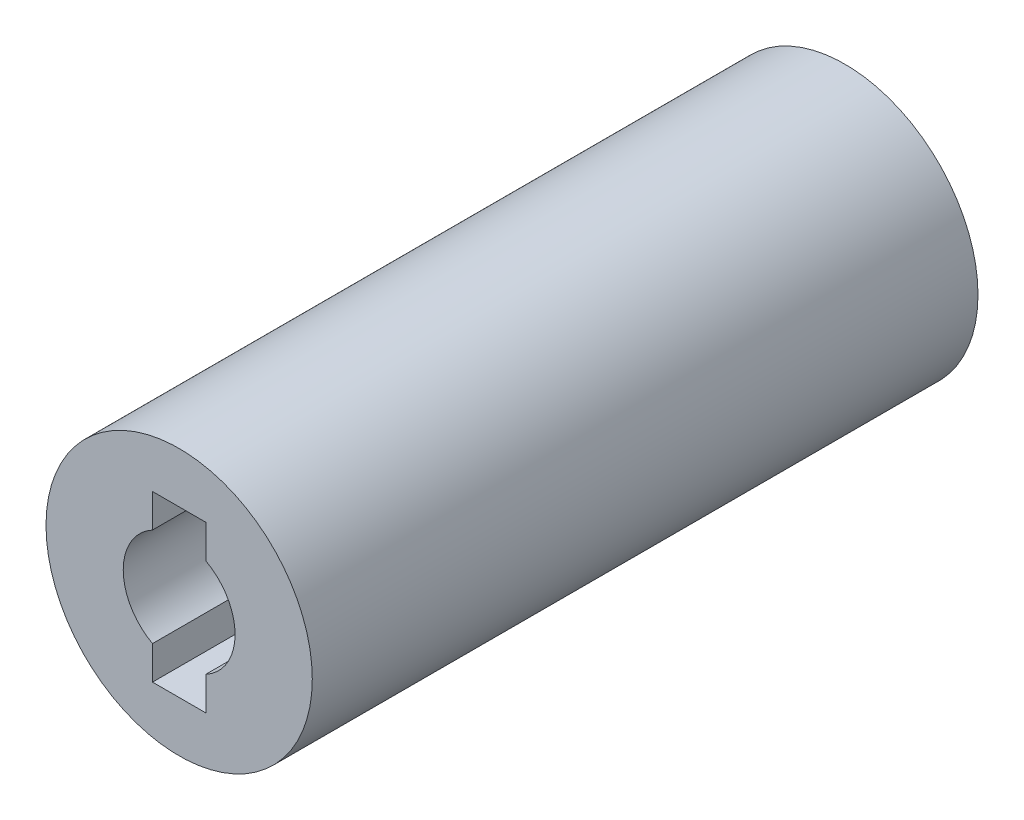
SolidWorks part; units mm, degrees
ref_plane "Front Plane" through (0, 0, 0) normal (0, 0, 1) x (1, 0, 0)
ref_plane "Top Plane" through (0, 0, 0) normal (0, 1, 0) x (1, 0, 0)
ref_plane "Right Plane" through (0, 0, 0) normal (1, 0, 0) x (0, 0, -1)
sketch "Sketch1" plane through (0, 0, 0) normal (0, 0, 1) x (1, 0, 0)
  circle A0 centre (0, 0) radius 5
  dimension "D1" = 10
extrude "Boss-Extrude1" add sketch "Sketch1" along normal blind 25
sketch "Sketch2" plane through (0, 0, 25) normal (0, 0, 1) x (1, 0, 0)
  circle A0 centre (0, 0) radius 2.1
  dimension "D1" = 4.2
extrude "Cut-Extrude1" cut sketch "Sketch2" against normal blind 10
sketch "Sketch3" plane through (0, 0, 25) normal (0, 0, 1) x (1, 0, 0)
  line L1 (-1, 3.1) -> (1, 3.1)
  line L2 (-1, 3.1) -> (-1, -3.1)
  line L3 (-1, -3.1) -> (1, -3.1)
  line L4 (1, 3.1) -> (1, -3.1)
  point P4 (0, 3.1)
  point P5 (-1, 0)
  dimension "D1" = 2
  dimension "D2" = 6.2
extrude "Cut-Extrude2" cut sketch "Sketch3" against normal blind 10
